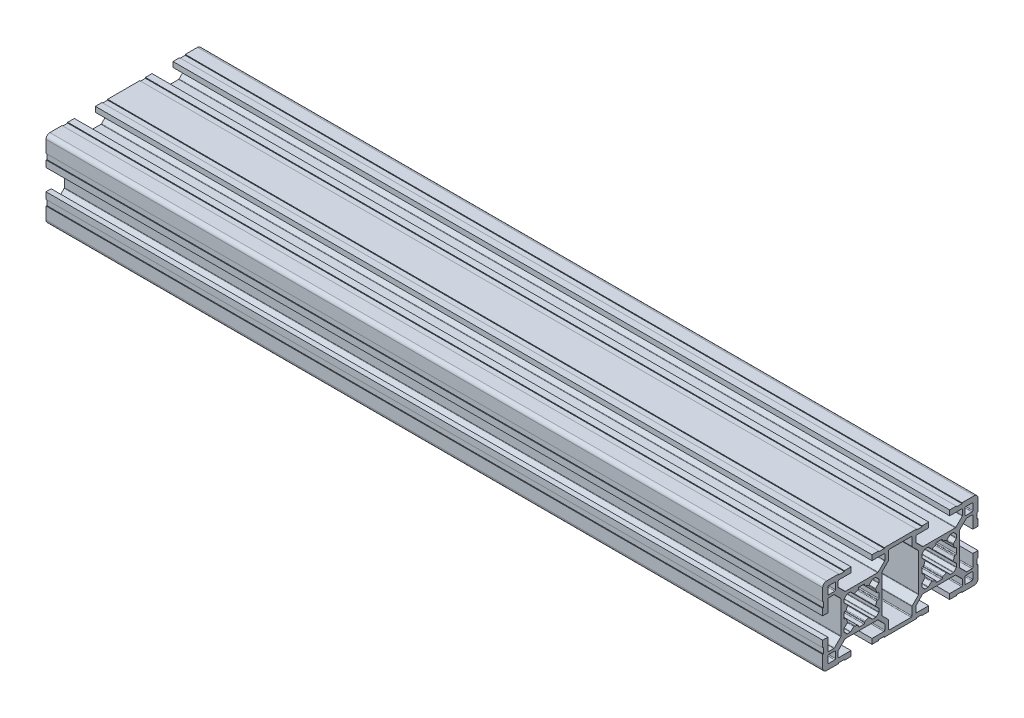
SolidWorks part; units mm, degrees
material "6063-T5 (Padrão)"
ref_plane "Plano frontal" through (0, 0, 0) normal (0, 0, 1) x (1, 0, 0)
ref_plane "Plano superior" through (0, 0, 0) normal (0, 1, 0) x (1, 0, 0)
ref_plane "Plano direito" through (0, 0, 0) normal (1, 0, 0) x (0, 0, -1)
sketch "Esboço1" plane through (0, 0, 0) normal (0, 0, 1) x (1, 0, 0)
  line L0 (-150, 0) -> (150, 0)
  point P4 (0, 0)
  dimension "D1" = 300
other "Retangular PF30-02 - PERFIL 3060 BÁSICO(1)"
ref_plane "Plano1" through (-150, 0, 0) normal (1, 0, 0) x (0, 1, 0)
sketch "Sketch11" plane through (-150, 0, 0) normal (1, 0, 0) x (0, 1, 0)
  line L0 (-9.8464, -4.5906) -> (-7.4222, -7.0149)
  line L1 (-7.21, -7.1028) -> (7.21, -7.1028)
  line L2 (7.4222, -7.0149) -> (9.8464, -4.5906)
  line L3 (10.0586, -4.5028) -> (13.2, -4.5028)
  line L4 (13.5, -4.2028) -> (13.5, 4.1972)
  line L5 (13.2, 4.4972) -> (10.0586, 4.4972)
  line L6 (9.8464, 4.5851) -> (7.4222, 7.0094)
  line L7 (7.21, 7.0972) -> (-7.21, 7.0972)
  line L8 (-7.4222, 7.0094) -> (-9.8464, 4.5851)
  line L9 (-10.0586, 4.4972) -> (-13.2, 4.4972)
  line L10 (-13.5, 4.1972) -> (-13.5, -4.2028)
  line L11 (-13.2, -4.5028) -> (-10.0586, -4.5028)
  line L12 (-6.7, 15.9528) -> (-6.7, 14.0528)
  line L13 (-6.1579, 16.2528) -> (-6.4, 16.2528)
  line L14 (-6.6121, 19.14) -> (-5.4871, 18.015)
  line L15 (-6.7, 20.4423) -> (-6.7, 19.3522)
  line L16 (-6.1319, 21.1347) -> (-6.6121, 20.6545)
  line L17 (-10.4678, 23.9149) -> (-7.9879, 21.435)
  line L18 (-12.7, 24.0028) -> (-10.6799, 24.0028)
  line L19 (-13, 19.0528) -> (-13, 23.7028)
  line L20 (-13, 19.0528) -> (-15, 19.0528)
  line L21 (6.7, 15.9528) -> (6.7, 14.0528)
  line L22 (7.9, 21.2229) -> (7.9, 8.7827)
  line L23 (15, 21.6028) -> (15, 19.0528)
  line L24 (-5.4396, 21.7028) -> (-4.3494, 21.7028)
  line L25 (-13, 25.3028) -> (-13, 27.7028)
  line L26 (-4.05, 28.0028) -> (-8.7, 28.0028)
  line L27 (-12.7, 28.0028) -> (-10.3, 28.0028)
  line L28 (-9, 27.7028) -> (-9, 25.6827)
  line L29 (-10, 27.7028) -> (-10, 25.3028)
  line L30 (-8.9121, 25.4705) -> (-6.4322, 22.9906)
  line L31 (15, 23.8028) -> (14.7, 23.8028)
  line L32 (14.7, 23.8028) -> (14.7, 21.6028)
  line L33 (15, 28.5028) -> (15, 23.8028)
  line L34 (8.8, 30.0028) -> (13.5, 30.0028)
  line L35 (8.8, 29.7028) -> (6.6, 29.7028)
  line L36 (4.05, 30.0028) -> (6.6, 30.0028)
  line L37 (4.05, 28.0028) -> (4.05, 30.0028)
  line L38 (10.3, 25.0028) -> (12.7, 25.0028)
  line L39 (15, 21.6028) -> (14.7, 21.6028)
  line L40 (6.6, 30.0028) -> (6.6, 29.7028)
  line L41 (-6.1319, 21.1347) -> (-5.6517, 21.6149)
  line L42 (-4.1373, 21.6149) -> (-3.0123, 20.4899)
  line L43 (-1.25, 21.1607) -> (-1.25, 21.4028)
  line L44 (8.8, 30.0028) -> (8.8, 29.7028)
  line L45 (1.25, 21.1607) -> (1.25, 21.4028)
  line L46 (4.1373, 21.6149) -> (3.0123, 20.4899)
  line L47 (6.1319, 21.1347) -> (5.6517, 21.6149)
  line L48 (8.9121, 25.4705) -> (6.4322, 22.9906)
  line L49 (10, 27.7028) -> (10, 25.3028)
  line L50 (9, 27.7028) -> (9, 25.6827)
  line L51 (12.7, 28.0028) -> (10.3, 28.0028)
  line L52 (4.05, 28.0028) -> (8.7, 28.0028)
  line L53 (13, 25.3028) -> (13, 27.7028)
  line L54 (5.4396, 21.7028) -> (4.3494, 21.7028)
  line L55 (13, 19.0528) -> (15, 19.0528)
  line L56 (13, 19.0528) -> (13, 23.7028)
  line L57 (12.7, 24.0028) -> (10.6799, 24.0028)
  line L58 (10.4678, 23.9149) -> (7.9879, 21.435)
  line L59 (6.1319, 21.1347) -> (6.6121, 20.6545)
  line L60 (6.7, 20.4423) -> (6.7, 19.3522)
  line L61 (6.6121, 19.14) -> (5.4871, 18.015)
  line L62 (6.1579, 16.2528) -> (6.4, 16.2528)
  line L63 (-7.9, 8.7827) -> (-7.9, 21.2229)
  line L64 (-0.95, 8.3028) -> (0.95, 8.3028)
  line L65 (-15, 8.4028) -> (-15, 10.9528)
  line L66 (-15, 6.2028) -> (-14.7, 6.2028)
  line L67 (-14.7, 6.2028) -> (-14.7, 8.4028)
  line L68 (-15, -14.9972) -> (15, -14.9972) construction
  line L69 (-6.1579, -13.7472) -> (-6.4, -13.7472)
  line L70 (-6.6121, -10.86) -> (-5.4871, -11.985)
  line L71 (-6.7, -9.5577) -> (-6.7, -10.6478)
  line L72 (-15, 8.4028) -> (-14.7, 8.4028)
  line L73 (-0.95, -21.6972) -> (0.95, -21.6972)
  line L74 (-6.1319, -8.8653) -> (-6.6121, -9.3455)
  line L75 (6.1579, 13.7528) -> (6.4, 13.7528)
  line L76 (6.6121, 10.8655) -> (5.4871, 11.9905)
  line L77 (6.7, 9.5632) -> (6.7, 10.6534)
  line L78 (6.1319, 8.8709) -> (6.6121, 9.3511)
  line L79 (10.4678, 6.0906) -> (7.9879, 8.5705)
  line L80 (12.7, 6.0028) -> (10.6799, 6.0028)
  line L81 (13, 10.9528) -> (13, 6.3028)
  line L82 (13, 10.9528) -> (15, 10.9528)
  line L83 (5.4396, 8.3028) -> (4.3494, 8.3028)
  line L84 (-10.4678, -6.0851) -> (-7.9879, -8.565)
  line L85 (-8.8, 30.0028) -> (-8.8, 29.7028)
  line L86 (-12.7, -5.9972) -> (-10.6799, -5.9972)
  line L87 (-13, -10.9472) -> (-13, -6.2972)
  line L88 (-13, -10.9472) -> (-15, -10.9472)
  line L89 (15, -8.3972) -> (15, -10.9472)
  line L90 (-5.4396, -8.2972) -> (-4.3494, -8.2972)
  line L91 (6.1319, 8.8709) -> (5.6517, 8.3906)
  line L92 (4.1373, 8.3906) -> (3.0123, 9.5156)
  line L93 (1.25, 8.8448) -> (1.25, 8.6028)
  line L94 (-15, -21.5972) -> (-15, -19.0472)
  line L95 (-6.6, 30.0028) -> (-6.6, 29.7028)
  line L96 (-1.25, 8.8448) -> (-1.25, 8.6028)
  line L97 (-4.1373, 8.3906) -> (-3.0123, 9.5156)
  line L98 (-6.1319, 8.8709) -> (-5.6517, 8.3906)
  line L99 (-15, -23.7972) -> (-14.7, -23.7972)
  line L100 (15, 8.4028) -> (14.7, 8.4028)
  line L101 (-14.7, -23.7972) -> (-14.7, -21.5972)
  line L102 (-15, -28.4972) -> (-15, -23.7972)
  line L103 (-8.8, -29.9972) -> (-13.5, -29.9972)
  line L104 (-8.8, -29.6972) -> (-6.6, -29.6972)
  line L105 (-4.05, -29.9972) -> (-6.6, -29.9972)
  line L106 (14.7, 6.2028) -> (14.7, 8.4028)
  line L107 (15, 6.2028) -> (14.7, 6.2028)
  line L108 (-4.05, -27.9972) -> (-4.05, -29.9972)
  line L109 (-10.3, -24.9972) -> (-12.7, -24.9972)
  line L110 (-6.2201, -22.8972) -> (6.2201, -22.8972)
  line L111 (-15, -21.5972) -> (-14.7, -21.5972)
  line L112 (15, -6.1972) -> (14.7, -6.1972)
  line L113 (-15, 21.6028) -> (-14.7, 21.6028)
  line L114 (-6.2201, 22.9028) -> (6.2201, 22.9028)
  line L115 (-10.3, 25.0028) -> (-12.7, 25.0028)
  line L116 (-4.05, 28.0028) -> (-4.05, 30.0028)
  line L117 (-4.05, 30.0028) -> (-6.6, 30.0028)
  line L118 (-8.8, 29.7028) -> (-6.6, 29.7028)
  line L119 (0, 29.9972) -> (0, -29.9972) construction
  line L120 (-15, 15.0028) -> (15, 15.0028) construction
  line L121 (-8.8, 30.0028) -> (-13.5, 30.0028)
  line L122 (-15, 28.5028) -> (-15, 23.8028)
  line L123 (-14.7, 23.8028) -> (-14.7, 21.6028)
  line L124 (-15, 23.8028) -> (-14.7, 23.8028)
  line L125 (-15, 21.6028) -> (-15, 19.0528)
  line L126 (14.7, -6.1972) -> (14.7, -8.3972)
  line L127 (-5.4396, 8.3028) -> (-4.3494, 8.3028)
  line L128 (15, 8.4028) -> (15, 10.9528)
  line L129 (15, 6.2028) -> (15, -6.1972)
  line L130 (-13, 10.9528) -> (-15, 10.9528)
  line L131 (-13, 10.9528) -> (-13, 6.3028)
  line L132 (-12.7, 6.0028) -> (-10.6799, 6.0028)
  line L133 (-10.4678, 6.0906) -> (-7.9879, 8.5705)
  line L134 (-6.1319, 8.8709) -> (-6.6121, 9.3511)
  line L135 (-0.95, 21.7028) -> (0.95, 21.7028)
  line L136 (-6.7, 9.5632) -> (-6.7, 10.6534)
  line L137 (-6.6121, 10.8655) -> (-5.4871, 11.9905)
  line L138 (-6.1579, 13.7528) -> (-6.4, 13.7528)
  line L139 (15, 0.0028) -> (-15, 0.0028) construction
  line L140 (15, -8.3972) -> (14.7, -8.3972)
  line L141 (-6.1319, -8.8653) -> (-5.6517, -8.3851)
  line L142 (-4.1373, -8.3851) -> (-3.0123, -9.5101)
  line L143 (-1.25, -8.8393) -> (-1.25, -8.5972)
  line L144 (-6.6, -29.9972) -> (-6.6, -29.6972)
  line L145 (1.25, -8.8393) -> (1.25, -8.5972)
  line L146 (4.1373, -8.3851) -> (3.0123, -9.5101)
  line L147 (6.1319, -8.8653) -> (5.6517, -8.3851)
  line L148 (-8.8, -29.9972) -> (-8.8, -29.6972)
  line L149 (5.4396, -8.2972) -> (4.3494, -8.2972)
  line L150 (13, -10.9472) -> (15, -10.9472)
  line L151 (13, -10.9472) -> (13, -6.2972)
  line L152 (12.7, -5.9972) -> (10.6799, -5.9972)
  line L153 (10.4678, -6.0851) -> (7.9879, -8.565)
  line L154 (6.1319, -8.8653) -> (6.6121, -9.3455)
  line L155 (6.7, -9.5577) -> (6.7, -10.6478)
  line L156 (6.6121, -10.86) -> (5.4871, -11.985)
  line L157 (6.1579, -13.7472) -> (6.4, -13.7472)
  line L158 (-15, -8.3972) -> (-14.7, -8.3972)
  line L159 (-15, 6.2028) -> (-15, -6.1972)
  line L160 (-14.7, -6.1972) -> (-14.7, -8.3972)
  line L161 (-15, -6.1972) -> (-14.7, -6.1972)
  line L162 (-15, -8.3972) -> (-15, -10.9472)
  line L163 (-0.95, -8.2972) -> (0.95, -8.2972)
  line L164 (-7.9, -8.7771) -> (-7.9, -21.2173)
  line L165 (6.1579, -16.2472) -> (6.4, -16.2472)
  line L166 (6.6121, -19.1345) -> (5.4871, -18.0095)
  line L167 (6.7, -20.4368) -> (6.7, -19.3466)
  line L168 (6.1319, -21.1291) -> (6.6121, -20.6489)
  line L169 (10.4678, -23.9094) -> (7.9879, -21.4295)
  line L170 (12.7, -23.9972) -> (10.6799, -23.9972)
  line L171 (13, -19.0472) -> (13, -23.6972)
  line L172 (13, -19.0472) -> (15, -19.0472)
  line L173 (5.4396, -21.6972) -> (4.3494, -21.6972)
  line L174 (13, -25.2972) -> (13, -27.6972)
  line L175 (4.05, -27.9972) -> (8.7, -27.9972)
  line L176 (12.7, -27.9972) -> (10.3, -27.9972)
  line L177 (9, -27.6972) -> (9, -25.6771)
  line L178 (10, -27.6972) -> (10, -25.2972)
  line L179 (8.9121, -25.465) -> (6.4322, -22.9851)
  line L180 (6.1319, -21.1291) -> (5.6517, -21.6093)
  line L181 (4.1373, -21.6093) -> (3.0123, -20.4844)
  line L182 (1.25, -21.1551) -> (1.25, -21.3972)
  line L183 (8.8, -29.9972) -> (8.8, -29.6972)
  line L184 (-1.25, -21.1551) -> (-1.25, -21.3972)
  line L185 (-4.1373, -21.6093) -> (-3.0123, -20.4844)
  line L186 (-6.1319, -21.1291) -> (-5.6517, -21.6093)
  line L187 (6.6, -29.9972) -> (6.6, -29.6972)
  line L188 (15, -21.5972) -> (14.7, -21.5972)
  line L189 (10.3, -24.9972) -> (12.7, -24.9972)
  line L190 (4.05, -27.9972) -> (4.05, -29.9972)
  line L191 (4.05, -29.9972) -> (6.6, -29.9972)
  line L192 (8.8, -29.6972) -> (6.6, -29.6972)
  line L193 (8.8, -29.9972) -> (13.5, -29.9972)
  line L194 (15, -28.4972) -> (15, -23.7972)
  line L195 (14.7, -23.7972) -> (14.7, -21.5972)
  line L196 (15, -23.7972) -> (14.7, -23.7972)
  line L197 (-8.9121, -25.465) -> (-6.4322, -22.9851)
  line L198 (-10, -27.6972) -> (-10, -25.2972)
  line L199 (-9, -27.6972) -> (-9, -25.6771)
  line L200 (-12.7, -27.9972) -> (-10.3, -27.9972)
  line L201 (-4.05, -27.9972) -> (-8.7, -27.9972)
  line L202 (-13, -25.2972) -> (-13, -27.6972)
  line L203 (-5.4396, -21.6972) -> (-4.3494, -21.6972)
  line L204 (15, -21.5972) -> (15, -19.0472)
  line L205 (7.9, -21.2173) -> (7.9, -8.7771)
  line L206 (6.7, -15.9472) -> (6.7, -14.0472)
  line L207 (-13, -19.0472) -> (-15, -19.0472)
  line L208 (-13, -19.0472) -> (-13, -23.6972)
  line L209 (-12.7, -23.9972) -> (-10.6799, -23.9972)
  line L210 (-10.4678, -23.9094) -> (-7.9879, -21.4295)
  line L211 (-6.1319, -21.1291) -> (-6.6121, -20.6489)
  line L212 (-6.7, -20.4368) -> (-6.7, -19.3466)
  line L213 (-6.6121, -19.1345) -> (-5.4871, -18.0095)
  line L214 (-6.1579, -16.2472) -> (-6.4, -16.2472)
  line L215 (-6.7, -15.9472) -> (-6.7, -14.0472)
  arc A0 (-9.8464, -4.5906) -> (-10.0586, -4.5028) centre (-10.0586, -4.8028) ccw
  arc A1 (-7.4222, -7.0149) -> (-7.21, -7.1028) centre (-7.21, -6.8028) ccw
  arc A2 (7.21, -7.1028) -> (7.4222, -7.0149) centre (7.21, -6.8028) ccw
  arc A3 (10.0586, -4.5028) -> (9.8464, -4.5906) centre (10.0586, -4.8028) ccw
  arc A4 (13.2, -4.5028) -> (13.5, -4.2028) centre (13.2, -4.2028) ccw
  arc A5 (13.5, 4.1972) -> (13.2, 4.4972) centre (13.2, 4.1972) ccw
  arc A6 (9.8464, 4.5851) -> (10.0586, 4.4972) centre (10.0586, 4.7972) ccw
  arc A7 (7.4222, 7.0094) -> (7.21, 7.0972) centre (7.21, 6.7972) ccw
  arc A8 (-7.21, 7.0972) -> (-7.4222, 7.0094) centre (-7.21, 6.7972) ccw
  arc A9 (-10.0586, 4.4972) -> (-9.8464, 4.5851) centre (-10.0586, 4.7972) ccw
  arc A10 (-13.2, 4.4972) -> (-13.5, 4.1972) centre (-13.2, 4.1972) ccw
  arc A11 (-13.5, -4.2028) -> (-13.2, -4.5028) centre (-13.2, -4.2028) ccw
  arc A12 (-6.4, 16.2528) -> (-6.7, 15.9528) centre (-6.4, 15.9528) ccw
  arc A13 (-5.867, 16.4795) -> (-6.1579, 16.2528) centre (-6.1579, 16.5528) cw
  arc A14 (-5.867, 16.4795) -> (-5.43, 17.6706) centre (0, 15.0028) cw
  arc A15 (-5.4871, 18.015) -> (-5.43, 17.6706) centre (-5.6993, 17.8029) cw
  arc A16 (-6.6121, 19.14) -> (-6.7, 19.3522) centre (-6.4, 19.3522) cw
  arc A17 (-6.6121, 20.6545) -> (-6.7, 20.4423) centre (-6.4, 20.4423) ccw
  arc A18 (-7.9879, 21.435) -> (-7.9, 21.2229) centre (-8.2, 21.2229) cw
  arc A19 (-10.6799, 24.0028) -> (-10.4678, 23.9149) centre (-10.6799, 23.7028) cw
  arc A20 (-13, 23.7028) -> (-12.7, 24.0028) centre (-12.7, 23.7028) cw
  arc A21 (13.5, 30.0028) -> (15, 28.5028) centre (13.5, 28.5028) cw
  arc A22 (1.25, 21.4028) -> (0.95, 21.7028) centre (0.95, 21.4028) ccw
  arc A23 (4.1373, 21.6149) -> (4.3494, 21.7028) centre (4.3494, 21.4028) cw
  arc A24 (1.4768, 20.8698) -> (1.25, 21.1607) centre (1.55, 21.1607) cw
  arc A25 (1.4768, 20.8698) -> (2.6678, 20.4328) centre (0, 15.0028) cw
  arc A26 (-10.3, 25.0028) -> (-10, 25.3028) centre (-10.3, 25.3028) ccw
  arc A27 (-6.4322, 22.9906) -> (-6.2201, 22.9028) centre (-6.2201, 23.2028) ccw
  arc A28 (-13, 25.3028) -> (-12.7, 25.0028) centre (-12.7, 25.3028) ccw
  arc A29 (-9, 25.6827) -> (-8.9121, 25.4705) centre (-8.7, 25.6827) ccw
  arc A30 (-10, 27.7028) -> (-10.3, 28.0028) centre (-10.3, 27.7028) ccw
  arc A31 (-8.7, 28.0028) -> (-9, 27.7028) centre (-8.7, 27.7028) ccw
  arc A32 (-12.7, 28.0028) -> (-13, 27.7028) centre (-12.7, 27.7028) ccw
  arc A33 (3.0123, 20.4899) -> (2.6678, 20.4328) centre (2.8001, 20.702) cw
  arc A34 (5.6517, 21.6149) -> (5.4396, 21.7028) centre (5.4396, 21.4028) ccw
  arc A35 (12.7, 28.0028) -> (13, 27.7028) centre (12.7, 27.7028) cw
  arc A36 (8.7, 28.0028) -> (9, 27.7028) centre (8.7, 27.7028) cw
  arc A37 (10, 27.7028) -> (10.3, 28.0028) centre (10.3, 27.7028) cw
  arc A38 (9, 25.6827) -> (8.9121, 25.4705) centre (8.7, 25.6827) cw
  arc A39 (13, 25.3028) -> (12.7, 25.0028) centre (12.7, 25.3028) cw
  arc A40 (6.4322, 22.9906) -> (6.2201, 22.9028) centre (6.2201, 23.2028) cw
  arc A41 (10.3, 25.0028) -> (10, 25.3028) centre (10.3, 25.3028) cw
  arc A42 (13, 23.7028) -> (12.7, 24.0028) centre (12.7, 23.7028) ccw
  arc A43 (10.6799, 24.0028) -> (10.4678, 23.9149) centre (10.6799, 23.7028) ccw
  arc A44 (7.9879, 21.435) -> (7.9, 21.2229) centre (8.2, 21.2229) ccw
  arc A45 (6.6121, 20.6545) -> (6.7, 20.4423) centre (6.4, 20.4423) cw
  arc A46 (6.6121, 19.14) -> (6.7, 19.3522) centre (6.4, 19.3522) ccw
  arc A47 (5.4871, 18.015) -> (5.43, 17.6706) centre (5.6993, 17.8029) ccw
  arc A48 (5.867, 16.4795) -> (5.43, 17.6706) centre (0, 15.0028) ccw
  arc A49 (5.867, 16.4795) -> (6.1579, 16.2528) centre (6.1579, 16.5528) ccw
  arc A50 (6.4, 16.2528) -> (6.7, 15.9528) centre (6.4, 15.9528) cw
  arc A51 (6.4, 13.7528) -> (6.7, 14.0528) centre (6.4, 14.0528) ccw
  arc A52 (-5.6517, 21.6149) -> (-5.4396, 21.7028) centre (-5.4396, 21.4028) cw
  arc A53 (-3.0123, 20.4899) -> (-2.6678, 20.4328) centre (-2.8001, 20.702) ccw
  arc A54 (-1.4768, 20.8698) -> (-2.6678, 20.4328) centre (0, 15.0028) ccw
  arc A55 (-1.4768, 20.8698) -> (-1.25, 21.1607) centre (-1.55, 21.1607) ccw
  arc A56 (-4.1373, 21.6149) -> (-4.3494, 21.7028) centre (-4.3494, 21.4028) ccw
  arc A57 (-6.4, 13.7528) -> (-6.7, 14.0528) centre (-6.4, 14.0528) cw
  arc A58 (-13.5, -29.9972) -> (-15, -28.4972) centre (-13.5, -28.4972) cw
  arc A59 (-1.25, 8.6028) -> (-0.95, 8.3028) centre (-0.95, 8.6028) ccw
  arc A60 (-4.1373, 8.3906) -> (-4.3494, 8.3028) centre (-4.3494, 8.6028) cw
  arc A61 (-1.4768, 9.1358) -> (-1.25, 8.8448) centre (-1.55, 8.8448) cw
  arc A62 (-1.4768, 9.1358) -> (-2.6678, 9.5728) centre (0, 15.0028) cw
  arc A63 (-3.0123, 9.5156) -> (-2.6678, 9.5728) centre (-2.8001, 9.3035) cw
  arc A64 (-5.6517, 8.3906) -> (-5.4396, 8.3028) centre (-5.4396, 8.6028) ccw
  arc A65 (5.867, 13.526) -> (6.1579, 13.7528) centre (6.1579, 13.4528) cw
  arc A66 (5.867, 13.526) -> (5.43, 12.3349) centre (0, 15.0028) cw
  arc A67 (5.4871, 11.9905) -> (5.43, 12.3349) centre (5.6993, 12.2026) cw
  arc A68 (6.6121, 10.8655) -> (6.7, 10.6534) centre (6.4, 10.6534) cw
  arc A69 (6.6121, 9.3511) -> (6.7, 9.5632) centre (6.4, 9.5632) ccw
  arc A70 (7.9879, 8.5705) -> (7.9, 8.7827) centre (8.2, 8.7827) cw
  arc A71 (10.6799, 6.0028) -> (10.4678, 6.0906) centre (10.6799, 6.3028) cw
  arc A72 (13, 6.3028) -> (12.7, 6.0028) centre (12.7, 6.3028) cw
  arc A73 (-5.867, -13.5205) -> (-6.1579, -13.7472) centre (-6.1579, -13.4472) cw
  arc A74 (-5.867, -13.5205) -> (-5.43, -12.3294) centre (0, -14.9972) cw
  arc A75 (-1.25, -21.3972) -> (-0.95, -21.6972) centre (-0.95, -21.3972) ccw
  arc A76 (-5.4871, -11.985) -> (-5.43, -12.3294) centre (-5.6993, -12.1971) cw
  arc A77 (-6.6121, -10.86) -> (-6.7, -10.6478) centre (-6.4, -10.6478) cw
  arc A78 (-6.6121, -9.3455) -> (-6.7, -9.5577) centre (-6.4, -9.5577) ccw
  arc A79 (-7.9879, -8.565) -> (-7.9, -8.7771) centre (-8.2, -8.7771) cw
  arc A80 (5.6517, 8.3906) -> (5.4396, 8.3028) centre (5.4396, 8.6028) cw
  arc A81 (3.0123, 9.5156) -> (2.6678, 9.5728) centre (2.8001, 9.3035) ccw
  arc A82 (-10.6799, -5.9972) -> (-10.4678, -6.0851) centre (-10.6799, -6.2972) cw
  arc A83 (-13, -6.2972) -> (-12.7, -5.9972) centre (-12.7, -6.2972) cw
  arc A84 (1.25, -8.5972) -> (0.95, -8.2972) centre (0.95, -8.5972) ccw
  arc A85 (4.1373, -8.3851) -> (4.3494, -8.2972) centre (4.3494, -8.5972) cw
  arc A86 (1.4768, -9.1302) -> (1.25, -8.8393) centre (1.55, -8.8393) cw
  arc A87 (1.4768, -9.1302) -> (2.6678, -9.5672) centre (0, -14.9972) cw
  arc A88 (3.0123, -9.5101) -> (2.6678, -9.5672) centre (2.8001, -9.2979) cw
  arc A89 (1.4768, 9.1358) -> (2.6678, 9.5728) centre (0, 15.0028) ccw
  arc A90 (1.4768, 9.1358) -> (1.25, 8.8448) centre (1.55, 8.8448) ccw
  arc A91 (4.1373, 8.3906) -> (4.3494, 8.3028) centre (4.3494, 8.6028) ccw
  arc A92 (1.25, 8.6028) -> (0.95, 8.3028) centre (0.95, 8.6028) cw
  arc A93 (5.6517, -8.3851) -> (5.4396, -8.2972) centre (5.4396, -8.5972) ccw
  arc A94 (-13, 6.3028) -> (-12.7, 6.0028) centre (-12.7, 6.3028) ccw
  arc A95 (-10.6799, 6.0028) -> (-10.4678, 6.0906) centre (-10.6799, 6.3028) ccw
  arc A96 (-7.9879, 8.5705) -> (-7.9, 8.7827) centre (-8.2, 8.7827) ccw
  arc A97 (-6.6121, 9.3511) -> (-6.7, 9.5632) centre (-6.4, 9.5632) cw
  arc A98 (-6.6121, 10.8655) -> (-6.7, 10.6534) centre (-6.4, 10.6534) ccw
  arc A99 (-5.4871, 11.9905) -> (-5.43, 12.3349) centre (-5.6993, 12.2026) ccw
  arc A100 (-1.25, 21.4028) -> (-0.95, 21.7028) centre (-0.95, 21.4028) cw
  arc A101 (-5.867, 13.526) -> (-5.43, 12.3349) centre (0, 15.0028) ccw
  arc A102 (-5.867, 13.526) -> (-6.1579, 13.7528) centre (-6.1579, 13.4528) ccw
  arc A103 (-13.5, 30.0028) -> (-15, 28.5028) centre (-13.5, 28.5028) ccw
  arc A104 (13, -6.2972) -> (12.7, -5.9972) centre (12.7, -6.2972) ccw
  arc A105 (10.6799, -5.9972) -> (10.4678, -6.0851) centre (10.6799, -6.2972) ccw
  arc A106 (7.9879, -8.565) -> (7.9, -8.7771) centre (8.2, -8.7771) ccw
  arc A107 (6.6121, -9.3455) -> (6.7, -9.5577) centre (6.4, -9.5577) cw
  arc A108 (6.6121, -10.86) -> (6.7, -10.6478) centre (6.4, -10.6478) ccw
  arc A109 (5.4871, -11.985) -> (5.43, -12.3294) centre (5.6993, -12.1971) ccw
  arc A110 (5.867, -13.5205) -> (5.43, -12.3294) centre (0, -14.9972) ccw
  arc A111 (5.867, -13.5205) -> (6.1579, -13.7472) centre (6.1579, -13.4472) ccw
  arc A112 (-5.6517, -8.3851) -> (-5.4396, -8.2972) centre (-5.4396, -8.5972) cw
  arc A113 (-3.0123, -9.5101) -> (-2.6678, -9.5672) centre (-2.8001, -9.2979) ccw
  arc A114 (-1.4768, -9.1302) -> (-2.6678, -9.5672) centre (0, -14.9972) ccw
  arc A115 (-1.4768, -9.1302) -> (-1.25, -8.8393) centre (-1.55, -8.8393) ccw
  arc A116 (-4.1373, -8.3851) -> (-4.3494, -8.2972) centre (-4.3494, -8.5972) ccw
  arc A117 (-1.25, -8.5972) -> (-0.95, -8.2972) centre (-0.95, -8.5972) cw
  arc A118 (-6.4, -13.7472) -> (-6.7, -14.0472) centre (-6.4, -14.0472) ccw
  arc A119 (-4.1373, -21.6093) -> (-4.3494, -21.6972) centre (-4.3494, -21.3972) cw
  arc A120 (-1.4768, -20.8642) -> (-1.25, -21.1551) centre (-1.55, -21.1551) cw
  arc A121 (-1.4768, -20.8642) -> (-2.6678, -20.4272) centre (0, -14.9972) cw
  arc A122 (-3.0123, -20.4844) -> (-2.6678, -20.4272) centre (-2.8001, -20.6965) cw
  arc A123 (-5.6517, -21.6093) -> (-5.4396, -21.6972) centre (-5.4396, -21.3972) ccw
  arc A124 (6.4, -13.7472) -> (6.7, -14.0472) centre (6.4, -14.0472) cw
  arc A125 (6.4, -16.2472) -> (6.7, -15.9472) centre (6.4, -15.9472) ccw
  arc A126 (5.867, -16.474) -> (6.1579, -16.2472) centre (6.1579, -16.5472) cw
  arc A127 (5.867, -16.474) -> (5.43, -17.6651) centre (0, -14.9972) cw
  arc A128 (5.4871, -18.0095) -> (5.43, -17.6651) centre (5.6993, -17.7974) cw
  arc A129 (6.6121, -19.1345) -> (6.7, -19.3466) centre (6.4, -19.3466) cw
  arc A130 (6.6121, -20.6489) -> (6.7, -20.4368) centre (6.4, -20.4368) ccw
  arc A131 (7.9879, -21.4295) -> (7.9, -21.2173) centre (8.2, -21.2173) cw
  arc A132 (10.6799, -23.9972) -> (10.4678, -23.9094) centre (10.6799, -23.6972) cw
  arc A133 (13, -23.6972) -> (12.7, -23.9972) centre (12.7, -23.6972) cw
  arc A134 (10.3, -24.9972) -> (10, -25.2972) centre (10.3, -25.2972) ccw
  arc A135 (6.4322, -22.9851) -> (6.2201, -22.8972) centre (6.2201, -23.1972) ccw
  arc A136 (13, -25.2972) -> (12.7, -24.9972) centre (12.7, -25.2972) ccw
  arc A137 (9, -25.6771) -> (8.9121, -25.465) centre (8.7, -25.6771) ccw
  arc A138 (10, -27.6972) -> (10.3, -27.9972) centre (10.3, -27.6972) ccw
  arc A139 (8.7, -27.9972) -> (9, -27.6972) centre (8.7, -27.6972) ccw
  arc A140 (12.7, -27.9972) -> (13, -27.6972) centre (12.7, -27.6972) ccw
  arc A141 (5.6517, -21.6093) -> (5.4396, -21.6972) centre (5.4396, -21.3972) cw
  arc A142 (3.0123, -20.4844) -> (2.6678, -20.4272) centre (2.8001, -20.6965) ccw
  arc A143 (-12.7, -27.9972) -> (-13, -27.6972) centre (-12.7, -27.6972) cw
  arc A144 (-8.7, -27.9972) -> (-9, -27.6972) centre (-8.7, -27.6972) cw
  arc A145 (-10, -27.6972) -> (-10.3, -27.9972) centre (-10.3, -27.6972) cw
  arc A146 (-9, -25.6771) -> (-8.9121, -25.465) centre (-8.7, -25.6771) cw
  arc A147 (-13, -25.2972) -> (-12.7, -24.9972) centre (-12.7, -25.2972) cw
  arc A148 (-6.4322, -22.9851) -> (-6.2201, -22.8972) centre (-6.2201, -23.1972) cw
  arc A149 (-10.3, -24.9972) -> (-10, -25.2972) centre (-10.3, -25.2972) cw
  arc A150 (1.4768, -20.8642) -> (2.6678, -20.4272) centre (0, -14.9972) ccw
  arc A151 (1.4768, -20.8642) -> (1.25, -21.1551) centre (1.55, -21.1551) ccw
  arc A152 (4.1373, -21.6093) -> (4.3494, -21.6972) centre (4.3494, -21.3972) ccw
  arc A153 (1.25, -21.3972) -> (0.95, -21.6972) centre (0.95, -21.3972) cw
  arc A154 (13.5, -29.9972) -> (15, -28.4972) centre (13.5, -28.4972) ccw
  arc A155 (-13, -23.6972) -> (-12.7, -23.9972) centre (-12.7, -23.6972) ccw
  arc A156 (-10.6799, -23.9972) -> (-10.4678, -23.9094) centre (-10.6799, -23.6972) ccw
  arc A157 (-7.9879, -21.4295) -> (-7.9, -21.2173) centre (-8.2, -21.2173) ccw
  arc A158 (-6.6121, -20.6489) -> (-6.7, -20.4368) centre (-6.4, -20.4368) cw
  arc A159 (-6.6121, -19.1345) -> (-6.7, -19.3466) centre (-6.4, -19.3466) ccw
  arc A160 (-5.4871, -18.0095) -> (-5.43, -17.6651) centre (-5.6993, -17.7974) ccw
  arc A161 (-5.867, -16.474) -> (-5.43, -17.6651) centre (0, -14.9972) ccw
  arc A162 (-5.867, -16.474) -> (-6.1579, -16.2472) centre (-6.1579, -16.5472) ccw
  arc A163 (-6.4, -16.2472) -> (-6.7, -15.9472) centre (-6.4, -15.9472) cw
  point P36 (-15, -14.9972)
  point P37 (0, 15.0028)
  point P66 (-11.6899, 24.0028)
  point P156 (0, 30.0028)
  point P176 (15, 30.0028)
  point P177 (11.6899, 24.0028)
  point P179 (-6.7, 15.0028)
  point P180 (6.7, 15.0028)
  point P187 (0, -0.0028)
  point P291 (15, -14.9972)
  point P315 (0, 29.9972)
  point P317 (15, 15.0028)
  point P321 (-15, 15.0028)
  point P322 (-15, 30.0028)
  point P324 (0, 15.0028)
  point P357 (-15, 0.0028)
  point P358 (0, 0.0083)
  point P359 (11.6899, 6.0028)
  point P360 (15, 0.0028)
  point P361 (0, 0.0028)
  point P362 (-11.6899, 6.0028)
  point P534 (0, -14.9972)
  point P539 (-15, -29.9972)
  point P557 (-11.6899, -5.9972)
  point P558 (11.6899, -5.9972)
  point P559 (0, -29.9917)
  point P560 (6.7, -14.9972)
  point P561 (-6.7, -14.9972)
  point P562 (11.6899, -23.9972)
  point P563 (15, -29.9972)
  point P564 (0, -29.9972)
  point P565 (-11.6899, -23.9972)
  point P566 (0, 0)
